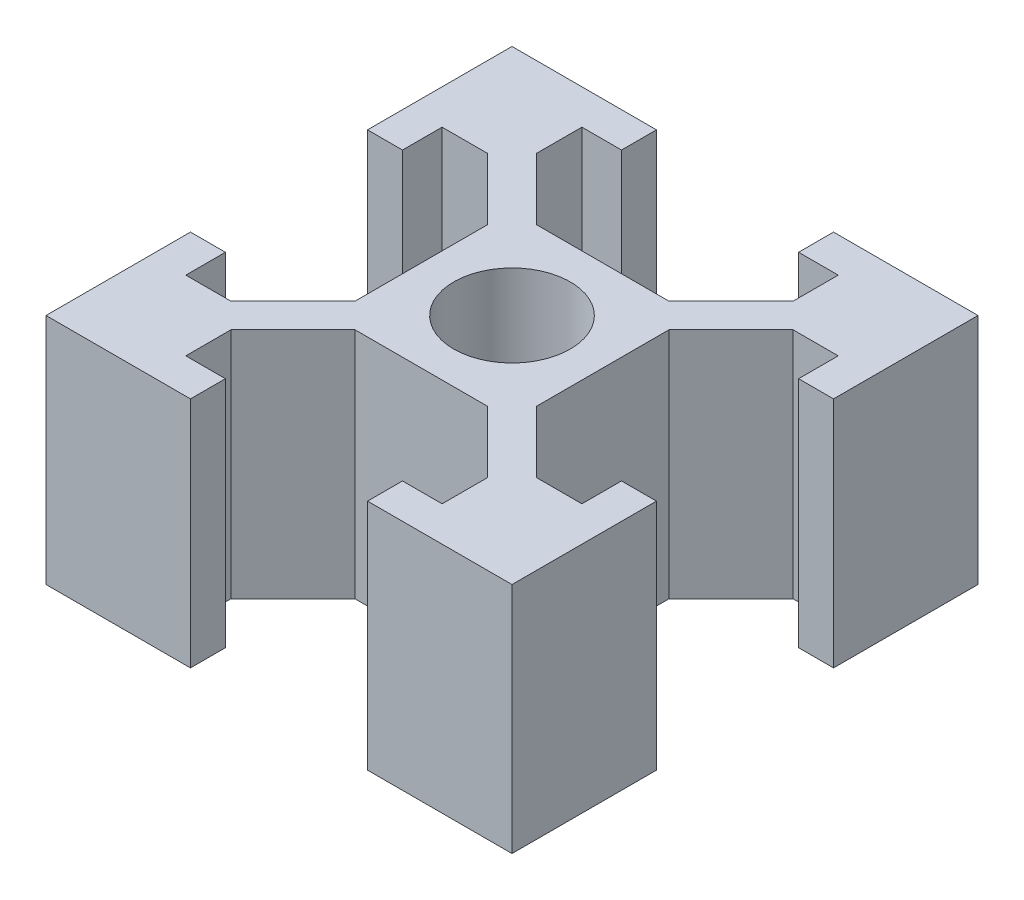
SolidWorks part; units mm, degrees
ref_plane "前视基准面" through (0, 0, 0) normal (0, 0, 1) x (1, 0, 0)
ref_plane "上视基准面" through (0, 0, 0) normal (0, 1, 0) x (1, 0, 0)
ref_plane "右视基准面" through (0, 0, 0) normal (1, 0, 0) x (0, 0, -1)
sketch "草图1" plane through (0, 0, 0) normal (0, 1, 0) x (1, 0, 0)
  line L0 (-6.5607, 5.5) -> (-3.9, 2.8393)
  line L1 (-10, 10) -> (10, 10)
  line L2 (-10, 10) -> (-10, -10)
  line L3 (-10, -10) -> (10, -10)
  line L4 (10, 10) -> (10, -10)
  line L5 (-10, 10) -> (10, -10) construction
  line L6 (-10, -10) -> (10, 10) construction
  line L7 (-3.9, 3.9) -> (3.9, 3.9)
  line L8 (-3.9, 3.9) -> (-3.9, -3.9)
  line L9 (-3.9, -3.9) -> (3.9, -3.9)
  line L10 (3.9, 3.9) -> (3.9, -3.9)
  line L11 (-3.9, 3.9) -> (3.9, -3.9) construction
  line L12 (-3.9, -3.9) -> (3.9, 3.9) construction
  line L13 (-10, 10) -> (-5.5, 10)
  line L14 (-10, 10) -> (-10, 5.5)
  line L15 (-10, 5.5) -> (-5.5, 5.5)
  line L16 (-5.5, 10) -> (-5.5, 5.5)
  line L17 (-10, 5.5) -> (-8.5, 5.5)
  line L18 (-10, 5.5) -> (-10, 3.8)
  line L19 (-10, 3.8) -> (-8.5, 3.8)
  line L20 (-8.5, 5.5) -> (-8.5, 3.8)
  line L21 (-5.5, 6.5607) -> (-2.8393, 3.9)
  line L22 (-3.8, 10) -> (-3.8, 8.5)
  line L23 (-5.5, 8.5) -> (-3.8, 8.5)
  line L24 (0, 10) -> (0, -10) construction
  line L25 (5.5, 8.5) -> (3.8, 8.5)
  line L26 (3.8, 10) -> (3.8, 8.5)
  line L27 (5.5, 6.5607) -> (2.8393, 3.9)
  line L28 (6.5607, 5.5) -> (3.9, 2.8393)
  line L29 (10, 3.8) -> (8.5, 3.8)
  line L30 (8.5, 5.5) -> (8.5, 3.8)
  line L31 (10, 5.5) -> (8.5, 5.5)
  line L32 (10, 5.5) -> (10, 3.8)
  line L33 (10, 5.5) -> (5.5, 5.5)
  line L34 (5.5, 10) -> (5.5, 5.5)
  line L35 (10, 10) -> (5.5, 10)
  line L36 (10, 10) -> (10, 5.5)
  line L37 (-10, 0) -> (10, 0) construction
  line L38 (-10, -3.8) -> (-8.5, -3.8)
  line L39 (-8.5, -5.5) -> (-8.5, -3.8)
  line L40 (-10, -5.5) -> (-5.5, -5.5)
  line L41 (-6.5607, -5.5) -> (-3.9, -2.8393)
  line L42 (-5.5, -6.5607) -> (-2.8393, -3.9)
  line L43 (-5.5, -10) -> (-5.5, -5.5)
  line L44 (-5.5, -8.5) -> (-3.8, -8.5)
  line L45 (-3.8, -10) -> (-3.8, -8.5)
  line L46 (3.8, -10) -> (3.8, -8.5)
  line L47 (6.5607, -5.5) -> (3.9, -2.8393)
  line L48 (5.5, -6.5607) -> (2.8393, -3.9)
  line L49 (-10, 10) -> (10, 10)
  line L50 (-10, -10) -> (10, -10)
  line L51 (5.5, -8.5) -> (3.8, -8.5)
  line L52 (5.5, -10) -> (5.5, -5.5)
  line L53 (10, -5.5) -> (5.5, -5.5)
  line L54 (10, -3.8) -> (8.5, -3.8)
  line L55 (8.5, -5.5) -> (8.5, -3.8)
  circle A0 centre (0, 0) radius 2.5
  dimension "D1" = 5
  dimension "D2" = 20
  dimension "D3" = 20
  dimension "D4" = 7.8
  dimension "D5" = 4.5
  dimension "D6" = 1.7
  dimension "D7" = 0.75
  dimension "D8" = 1.5
extrude "凸台-拉伸1" add sketch "草图1" along normal blind 10 contours L1 L34 L33 L31 L4 | L4 L31 L30 L29 | L34 L27 L7 L10 L28 L33 | L34 L1 L26 L25 | L10 L7 L8 L9 A0 | L16 L23 L22 L1 | L16 L1 L2 L15 | L20 L15 L2 L19 | L21 L16 L15 L0 L8 L7 | L3 L43 L40 L2 | L3 L45 L44 L43 | L2 L40 L39 L38 | L43 L42 L9 L8 L41 L40 | L53 L47 L10 L9 L48 L52 | L4 L53 L52 L50 | L55 L53 L4 L54 | L3 L52 L51 L46
